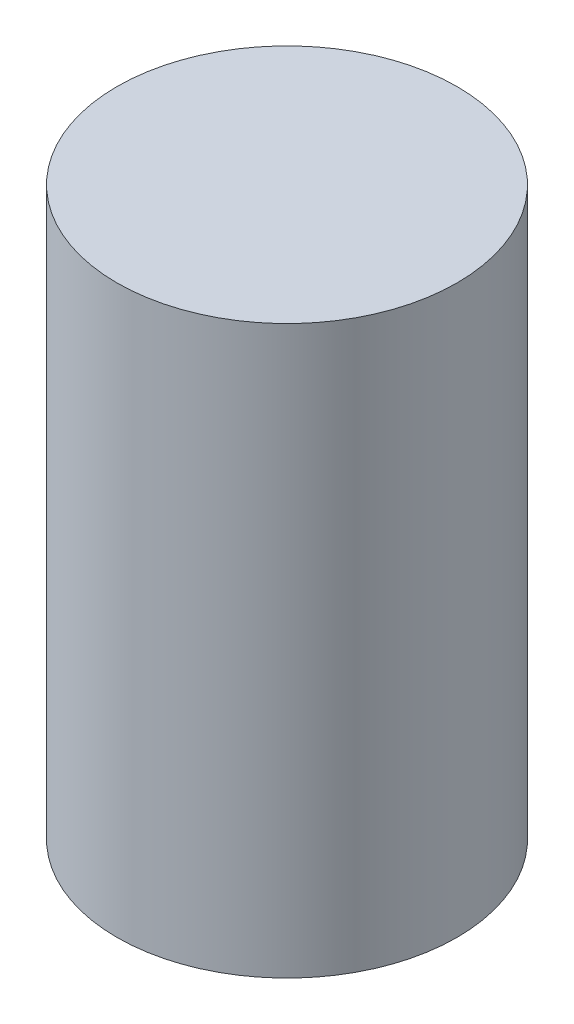
SolidWorks part; units mm, degrees
material "Chrome Stainless Steel"
ref_plane "Front Plane" through (0, 0, 0) normal (0, 0, 1) x (1, 0, 0)
ref_plane "Top Plane" through (0, 0, 0) normal (0, 1, 0) x (1, 0, 0)
ref_plane "Right Plane" through (0, 0, 0) normal (1, 0, 0) x (0, 0, -1)
sketch "Sketch1" plane through (0, 0, 0) normal (0, 1, 0) x (1, 0, 0)
  circle A0 centre (0, 0) radius 3.81
  dimension "D1" = 7.62
extrude "Boss-Extrude1" add sketch "Sketch1" along normal blind 12.7
